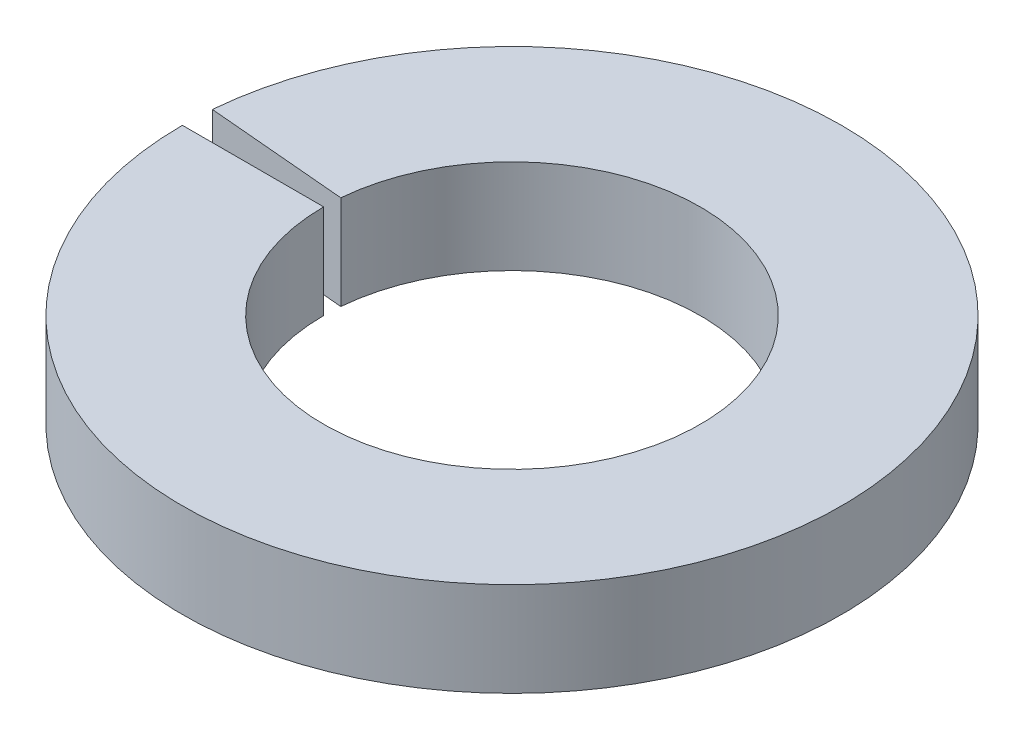
SolidWorks part; units mm, degrees
material "Zoltek Panex 33"
ref_plane "Front Plane" through (0, 0, 0) normal (0, 0, 1) x (1, 0, 0)
ref_plane "Top Plane" through (0, 0, 0) normal (0, 1, 0) x (1, 0, 0)
ref_plane "Right Plane" through (0, 0, 0) normal (1, 0, 0) x (0, 0, -1)
sketch "Sketch1" plane through (0, 0, 0) normal (0, 0, 1) x (1, 0, 0)
  line L0 (0, 0) -> (0, 3.175) construction
  line L2 (-11.1125, 0) -> (-6.35, 0)
  line L3 (-11.1125, 0) -> (-11.1125, 3.175)
  line L4 (-11.1125, 3.175) -> (-6.35, 3.175)
  line L5 (-6.35, 0) -> (-6.35, 3.175)
  dimension "D1" = 3.175
  dimension "D2" = 12.7
  dimension "D3" = 4.7625
revolve "Revolve1" add sketch "Sketch1" angle 355 about L0
